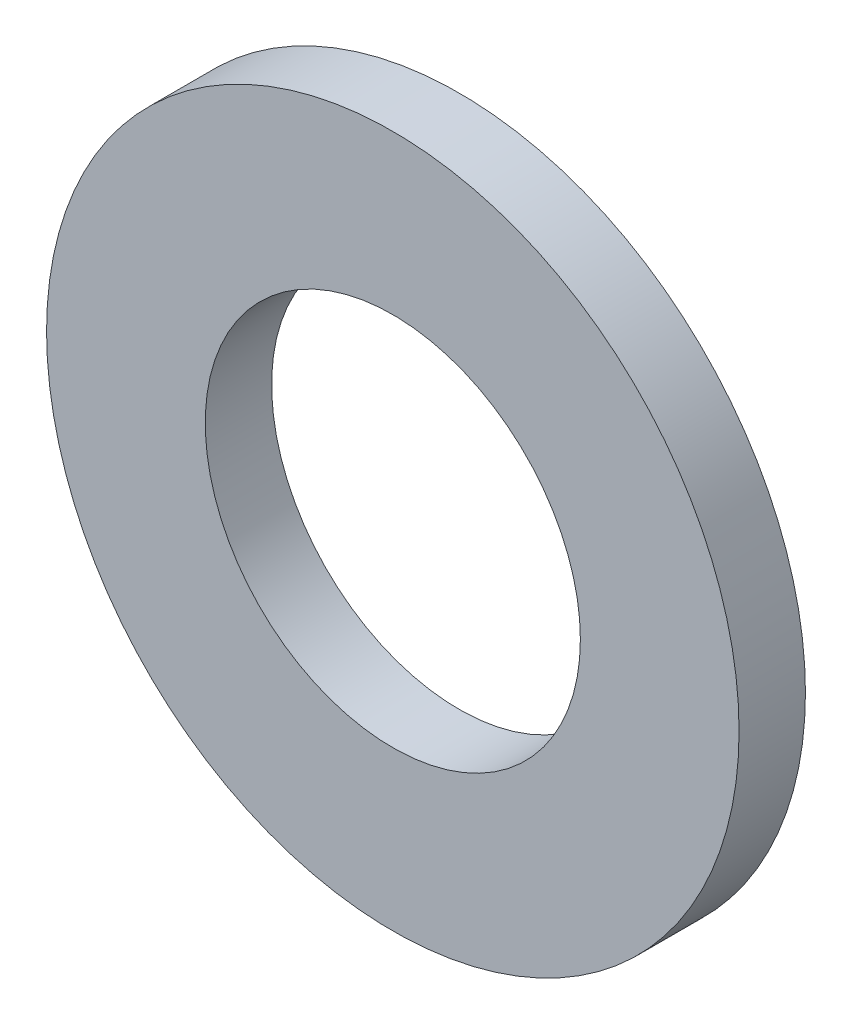
SolidWorks part; units mm, degrees
ref_plane "Front Plane" through (0, 0, 0) normal (0, 0, 1) x (1, 0, 0)
ref_plane "Top Plane" through (0, 0, 0) normal (0, 1, 0) x (1, 0, 0)
ref_plane "Right Plane" through (0, 0, 0) normal (1, 0, 0) x (0, 0, -1)
sketch "Sketch1" plane through (0, 0, 0) normal (0, 0, 1) x (1, 0, 0)
  circle A0 centre (0, 0) radius 6.5
  circle A1 centre (0, 0) radius 12
  dimension "ID" = 13
  dimension "OD" = 24
extrude "Extrude1" add sketch "Sketch1" against normal blind 2.3
